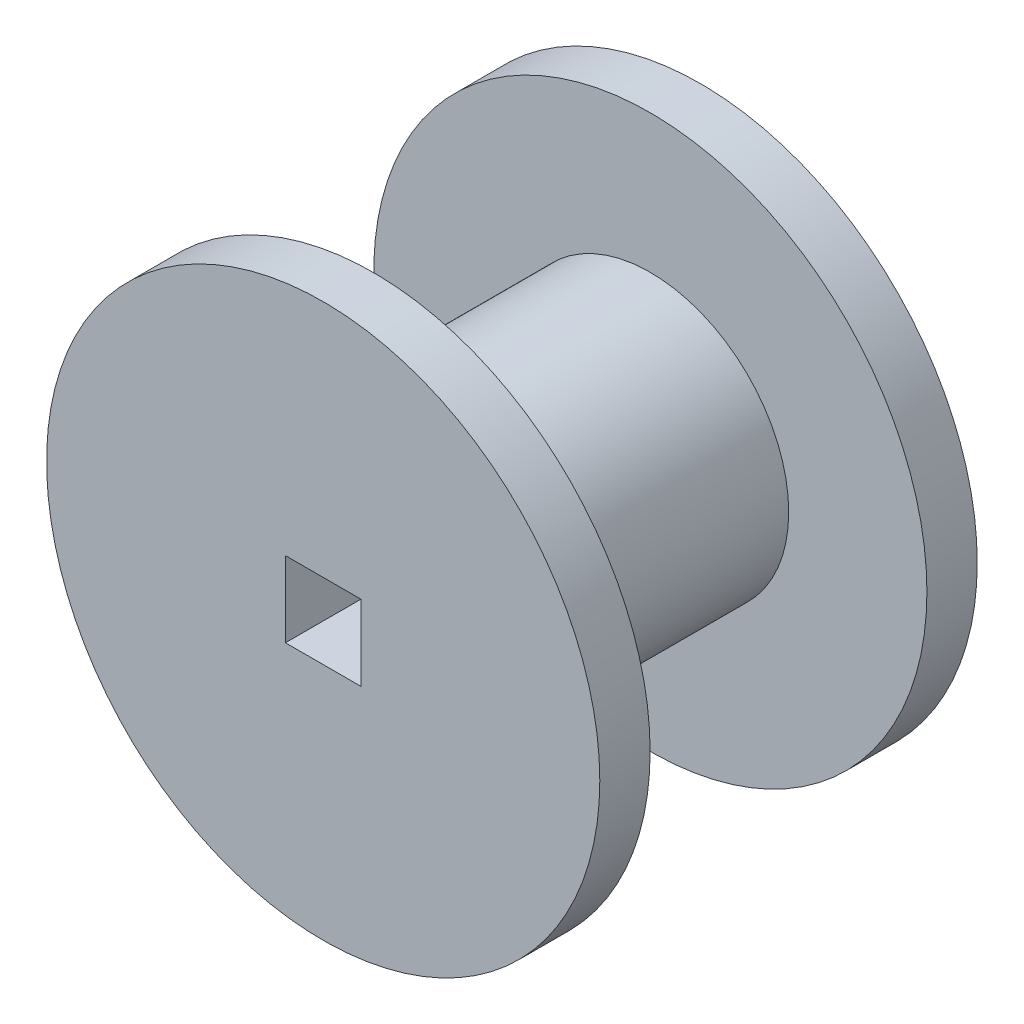
SolidWorks part; units mm, degrees
ref_plane "前视基准面" through (0, 0, 0) normal (0, 0, 1) x (1, 0, 0)
ref_plane "上视基准面" through (0, 0, 0) normal (0, 1, 0) x (1, 0, 0)
ref_plane "右视基准面" through (0, 0, 0) normal (1, 0, 0) x (0, 0, -1)
other "Configuration Table"
sketch "草图1" plane through (0, 0, 0) normal (0, 0, 1) x (1, 0, 0)
  line L1 (-1.5, -1.5) -> (1.5, -1.5)
  line L2 (-1.5, -1.5) -> (-1.5, 1.5)
  line L3 (-1.5, 1.5) -> (1.5, 1.5)
  line L4 (1.5, -1.5) -> (1.5, 1.5)
  line L5 (0, 1.5) -> (0, -1.5) construction
  line L6 (-1.5, 0) -> (1.5, 0) construction
  circle A0 centre (0, 0) radius 10.9926
  dimension "D1" = 3
  dimension "D2" = 3
extrude "凸台-拉伸1" add sketch "草图1" along normal blind 2
sketch "草图2" plane through (0, 0, 2) normal (0, 0, 1) x (1, 0, 0)
  line L1 (-1.5, -1.5) -> (1.5, -1.5)
  line L2 (-1.5, -1.5) -> (-1.5, 1.5)
  line L3 (-1.5, 1.5) -> (1.5, 1.5)
  line L4 (1.5, -1.5) -> (1.5, 1.5)
  line L5 (0, 1.5) -> (0, -1.5) construction
  line L6 (-1.5, 0) -> (1.5, 0) construction
  circle A0 centre (0, 0) radius 5.5
  point P0 (0, 0)
  dimension "D1" = 3
  dimension "D2" = 3
extrude "凸台-拉伸2" add sketch "草图2" along normal blind 5.5
mirror "镜向1" about plane through (0, 0, 7.5) normal (0, 0, 1) of "凸台-拉伸1", "凸台-拉伸2"
